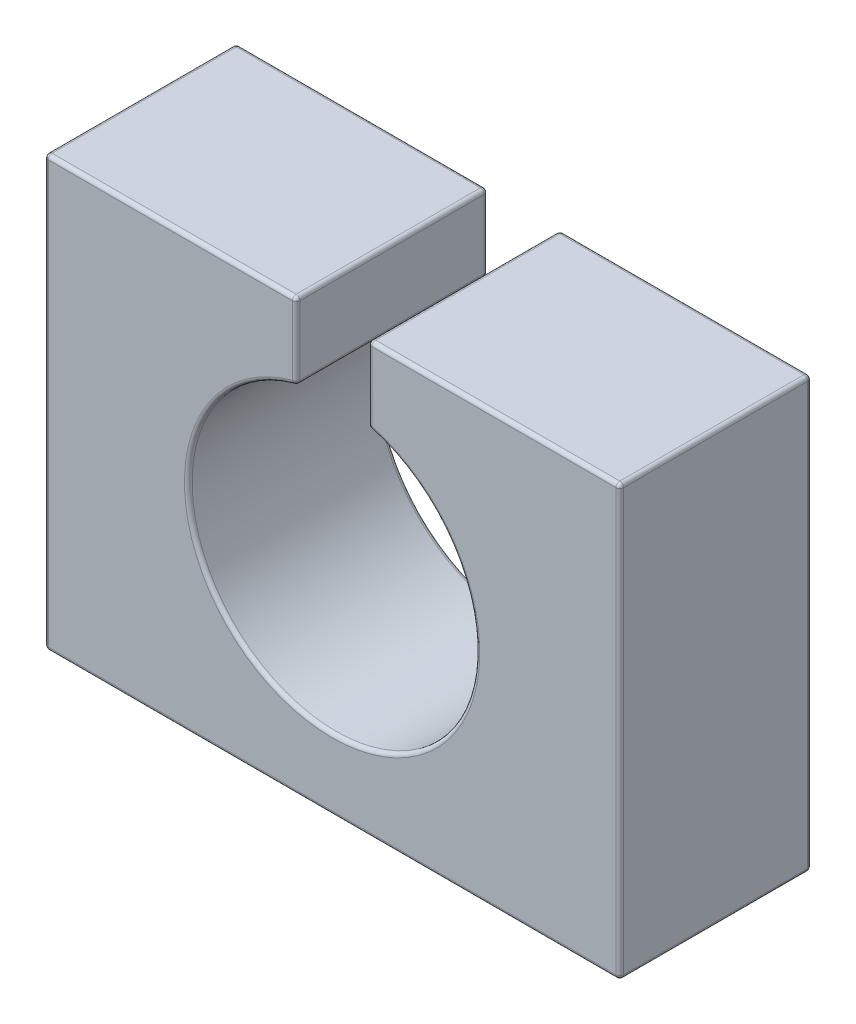
SolidWorks part; units mm, degrees
material "1060 Alloy"
ref_plane "Front Plane" through (0, 0, 0) normal (0, 0, 1) x (1, 0, 0)
ref_plane "Top Plane" through (0, 0, 0) normal (0, 1, 0) x (1, 0, 0)
ref_plane "Right Plane" through (0, 0, 0) normal (1, 0, 0) x (0, 0, -1)
sketch "Sketch1" plane through (0, 0, 0) normal (0, 0, 1) x (1, 0, 0)
  line L0 (0, 0) -> (38.1, 0)
  line L1 (38.1, 0) -> (38.1, 28.448)
  line L7 (0, 28.448) -> (0, 0)
  line L8 (19.05, 0) -> (19.05, 36.1275) construction
  line L9 (0, 28.448) -> (38.1, 28.448)
  dimension "D1" = 28.448
  dimension "D3" = 38.1
extrude "Boss-Extrude1" add sketch "Sketch1" against normal blind 12.7
sketch "Sketch3" plane through (0, 0, 0) normal (0, 0, 1) x (1, 0, 0)
  line L0 (19.05, 0) -> (19.05, 28.9356) construction
  line L1 (0, 0) -> (38.1, 0) construction
  line L2 (16.6687, 28.448) -> (16.6688, 23.4465)
  line L3 (38.1, 28.448) -> (0, 28.448) construction
  line L4 (16.6687, 28.448) -> (21.4312, 28.448)
  line L5 (21.4312, 28.448) -> (21.4312, 23.4465)
  line L6 (16.6687, 28.448) -> (21.4312, 28.448)
  line L7 (0, 28.448) -> (0, 0) construction
  arc A0 (16.6688, 23.4465) -> (21.4312, 23.4465) centre (19.05, 14.224) ccw
  line M8 (38.1, 28.448) -> (0, 28.448)
  dimension "D1" = 19.05
  dimension "D2" = 14.224
  dimension "D3" = 4.7625
  dimension "D4" = 16.6687
extrude "Cut-Extrude2" cut sketch "Sketch3" against normal up to next contours A0 L0 L6 L2 | L0 A0 L5 M8
fillet "Fillet1" radius 0.254 24 edges at (21.4312, 25.9473, -12.7) (21.4312, 28.448, -6.35) (29.7656, 28.448, -12.7) (38.1, 28.448, -6.35) (38.1, 14.224, -12.7) (21.4312, 25.9473, 0) (29.7656, 28.448, 0) (38.1, 14.224, 0) (8.3344, 28.448, 0) (8.3344, 28.448, -12.7) (0, 14.224, -12.7) (0, 28.448, -6.35) (0, 14.224, 0) (38.1, 0, -6.35) (19.05, 0, -12.7) (0, 0, -6.35) (19.05, 0, 0) (21.4312, 23.4465, -6.35) (19.05, 4.699, 0) (19.05, 4.699, -12.7) (16.6688, 23.4465, -6.35) (16.6688, 25.9473, 0) (16.6687, 28.448, -6.35) (16.6687, 25.9473, -12.7)
